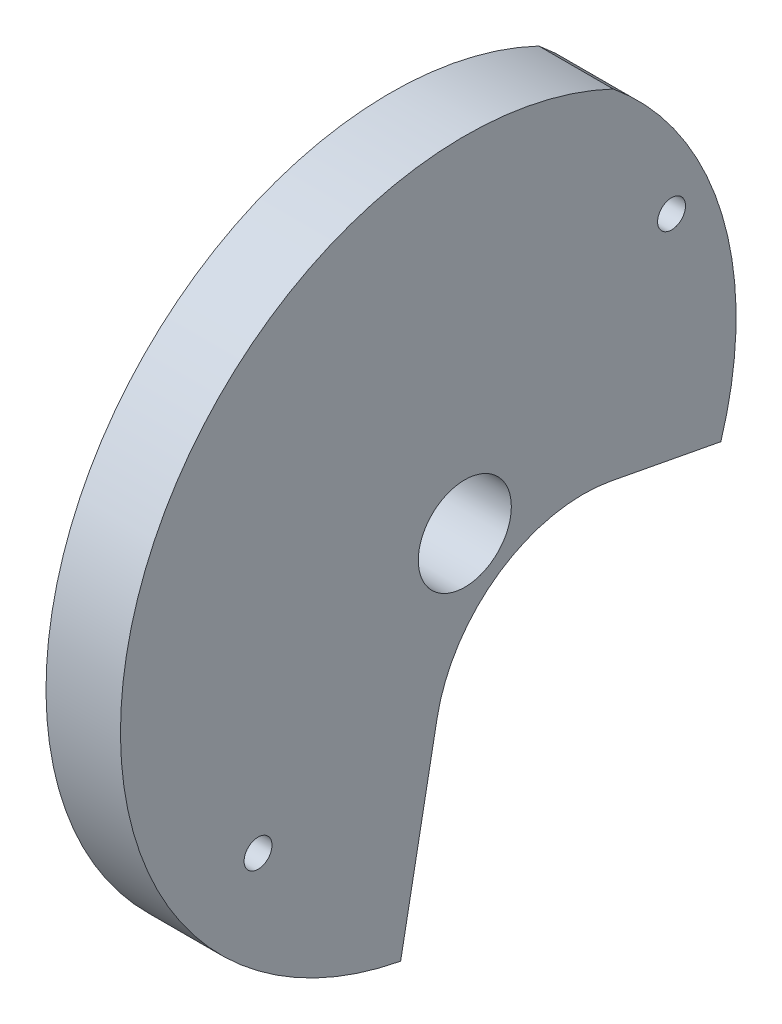
SolidWorks part; units mm, degrees
ref_plane "Спереди" through (0, 0, 0) normal (0, 0, 1) x (1, 0, 0)
ref_plane "Сверху" through (0, 0, 0) normal (0, 1, 0) x (1, 0, 0)
ref_plane "Справа" through (0, 0, 0) normal (1, 0, 0) x (0, 0, -1)
sketch "Эскиз1" plane through (0, 0, 0) normal (1, 0, 0) x (0, 0, -1)
  line L0 (-40, -19.3085) -> (40, -19.3085) construction
  line L1 (-40, -3.3085) -> (40, -3.3085) construction
  line L2 (0, 0) -> (-14.0648, -13.2364)
  line L3 (0, 0) -> (13.2364, -14.0648)
  line L10 (0, 0) -> (18.9755, -3.5985)
  line L11 (0, 0) -> (-3.5985, -18.9755)
  line L14 (0, 0) -> (-11.821, -15.2736) [skipped]
  line L15 (0, 0) -> (-9.2861, -16.9348) [skipped]
  line L16 (0, 0) -> (-6.5226, -18.179) [skipped]
  line L17 (0, 0) -> (-0.5858, -19.3048) [skipped]
  line L18 (0, 0) -> (19.3048, -0.5858) [skipped]
  line L19 (0, 0) -> (18.179, -6.5226) [skipped]
  line L20 (0, 0) -> (16.9348, -9.2861) [skipped]
  line L21 (0, 0) -> (15.2736, -11.821) [skipped]
  circle A0 centre (0, 0) radius 19.3137
  circle A1 centre (-0.3431, -11.3085) radius 8
  arc A11 (13.7548, -2.6085) -> (5.0514, 18.6414) centre (-3.4252, 2.7623) ccw
  circle A12 centre (0, 0) radius 2.5
  circle A13 centre (6.3694, -9.3505) radius 8
  point P24 (0, 0)
  point P46 (0, -19.3085)
  dimension "D10" = 18
  dimension "D13" = 5
  dimension "D4" = 16
  dimension "D1" = 16
  dimension "D3" = 80
  dimension "D9" = 14
  dimension "D2" = 6
extrude "Бобышка-Вытянуть1" add sketch "Эскиз1" along normal blind 4 contours A12 L10 A11 A0 L2 | L11 A1 | A1 L2 A0 L11 | A12 L2 A1 L11 | A13 L3 A12 L11 A1 | A13 L10 A12 L3 | A13 A1 L11
sketch "Эскиз2" plane through (4, 0, 0) normal (1, 0, 0) x (0, 0, -1)
  line L0 (-11.1076, -9.3204) -> (0, 0) construction
  line L1 (0, 0) -> (19.8052, 0) construction
  circle A0 centre (-11.1076, -9.3204) radius 0.75
  circle A1 centre (11.1076, 9.3204) radius 0.75
  point P10 (0, 0)
  dimension "D1" = 14.5
  dimension "D2" = 1.5
  dimension "D3" = 140
  dimension "D4" = 2
extrude "Вырез-Вытянуть1" cut sketch "Эскиз2" against normal blind 10
sketch "Эскиз3" plane through (4, 0, 0) normal (1, 0, 0) x (0, 0, -1)
  circle A0 centre (0, 0) radius 18.5
  circle A1 centre (0, 0) radius 25.4648
  dimension "D1" = 37
extrude "Вырез-Вытянуть2" cut sketch "Эскиз3" against normal blind 10
